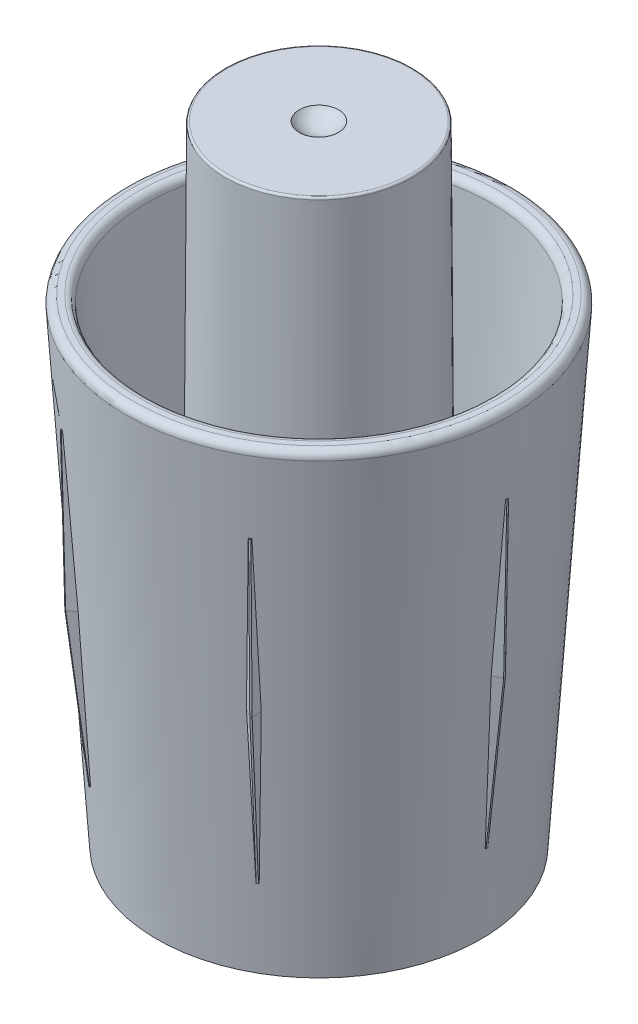
SolidWorks part; units mm, degrees
ref_plane "Front Plane" through (0, 0, 0) normal (0, 0, 1) x (1, 0, 0)
ref_plane "Top Plane" through (0, 0, 0) normal (0, 1, 0) x (1, 0, 0)
ref_plane "Right Plane" through (0, 0, 0) normal (1, 0, 0) x (0, 0, -1)
sketch "Sketch1" plane through (0, 0, 0) normal (0, 0, 1) x (1, 0, 0)
  line L0 (0, 0) -> (7.79, 0)
  line L1 (7.79, 0) -> (9.3, 22.95)
  line L2 (9.3, 22.95) -> (8.3, 22.95)
  line L3 (8.3, 22.95) -> (7.3459, 8.4492)
  line L4 (7.3459, 8.4492) -> (4.6, 13.16)
  line L5 (4.6, 13.16) -> (4.5, 30.16)
  line L6 (4.5, 30.16) -> (0, 30.16)
  line L7 (0, 30.16) -> (0, 29.16)
  line L8 (0, 29.16) -> (3.5, 29.16)
  line L9 (3.5, 29.16) -> (3.5941, 13.16)
  line L10 (3.5941, 13.16) -> (7.1848, 7)
  line L11 (7.1848, 7) -> (6.79, 1)
  line L12 (6.79, 1) -> (0, 1)
  line L13 (0, 1) -> (0, 0)
  dimension "D1" = 30.16
  dimension "D2" = 4.5
  dimension "D3" = 3.5
  dimension "D4" = 22.95
  dimension "D5" = 1
  dimension "D6" = 4.6
  dimension "D7" = 1
  dimension "D8" = 7.79
  dimension "D9" = 6.79
  dimension "D10" = 1
  dimension "D11" = 7
  dimension "D12" = 17
  dimension "D13" = 16
  dimension "D14" = 9.3
revolve "Revolve1" add sketch "Sketch1" angle 360 about L7
sketch "Sketch3" plane through (0, 0, 0) normal (0, 0, 1) x (1, 0, 0)
  line L0 (8.8104, 18.97) -> (8.6552, 11.47)
  line L1 (8.6552, 11.47) -> (7.8114, 3.97)
  line L2 (9.3, 22.95) -> (-9.3, 22.95) construction
  dimension "D1" = 15
  dimension "D2" = 7.5
  dimension "D3" = 3.98
ref_plane "Plane1" through (8.8104, 18.97, 0) normal (-0.0207, -0.9998, 0) x (-0.9998, 0.0207, 0)
sketch "Sketch4" plane through (8.8104, 18.97, 0) normal (-0.0207, -0.9998, 0) x (-0.9998, 0.0207, 0)
  line L1 (-0.266, -0.0413) -> (0.1711, -0.2936)
  line L2 (0.1711, -0.2936) -> (0.1711, 0.2936)
  line L3 (0.1711, 0.2936) -> (-0.266, 0.0413)
  circle A0 centre (0.0016, 0) radius 0.1695 construction
  arc A1 (-0.266, 0.0413) -> (-0.266, -0.0413) centre (-0.2248, 0) ccw
sweep "Sweep1" add profiles "Sketch4" path "Sketch3"
pattern_circular "CirPattern1" count 6 over 360 about axis through (0, 0, 0) along (0, 1, 0) of "Sweep1"
sketch "Sketch6" plane through (0, 0, 0) normal (0, -1, 0) x (-1, 0, 0)
  circle A0 centre (0, 0) radius 6.79
  dimension "D1" = 13.58
extrude "Cut-Extrude3" cut sketch "Sketch6" against normal blind 5
ref_plane "Plane2" through (0, 13.16, 0) normal (0, 1, 0) x (1, 0, 0)
sketch "Sketch7" plane through (0, 30.16, 0) normal (0, 1, 0) x (1, 0, 0)
  circle A0 centre (0, 0) radius 0.945
  point P3 (0.945, 0)
  point P4 (0, 0)
  dimension "D1" = 1.89
sketch "Sketch8" plane through (0, 0, 0) normal (0, 0, 1) x (1, 0, 0)
  line L0 (0, 30.16) -> (0, 29.71)
  line L1 (0.945, 30.16) -> (-0.945, 30.16) construction
  line L2 (0, 30.16) -> (0.945, 30.16)
  arc A0 (0, 29.71) -> (0.945, 30.16) centre (0, 30.9272) ccw
  dimension "D1" = 0.45
revolve "Cut-Revolve1" cut sketch "Sketch8" angle 360 about L0
sketch "Sketch9" plane through (0, 13.16, 0) normal (0, 1, 0) x (1, 0, 0)
  line L0 (0, 0) -> (0, 7.79) construction
  arc A0 (3.1615, 7.1196) -> (0.5166, 7.7729) centre (0, 0) ccw
  arc A1 (2.9585, 6.6627) -> (0.4834, 7.274) centre (0, 0) ccw
  arc A2 (-0.4834, 7.274) -> (-2.9585, 6.6627) centre (0, 0) ccw
  arc A3 (2.9585, 6.6627) -> (3.1615, 7.1196) centre (3.06, 6.8912) ccw
  arc A4 (0.5166, 7.7729) -> (0.4834, 7.274) centre (0.5, 7.5234) ccw
  arc A5 (-2.9585, 6.6627) -> (-3.1615, 7.1196) centre (-3.06, 6.8912) cw
  arc A6 (-0.5166, 7.7729) -> (-0.4834, 7.274) centre (-0.5, 7.5234) cw
  arc A7 (-0.5166, 7.7729) -> (-3.1615, 7.1196) centre (0, 0) ccw
  dimension "D1" = 15.58
  dimension "D2" = 14.58
  dimension "D4" = 2.56
  dimension "D5" = 0.5
sketch "Sketch10" plane through (0, 0, 0) normal (1, 0, 0) x (0, 0, -1)
  line L0 (7.136, 13.16) -> (6.4443, -0.0501)
  line L1 (7.7729, 13.16) -> (7.1196, 13.16) construction
  line L2 (0, 13.16) -> (7.79, 13.16) construction
sweep "Cut-Sweep1" cut profiles "Sketch9" path "Sketch10"
pattern_circular "CirPattern2" count 3 over 360 about axis through (0, 30.16, 0) along (0, 1, 0) of "Cut-Sweep1"
fillet "Fillet1" radius 0.1 1 edges at (-4.5, 30.16, 0)
fillet "Fillet2" radius 0.36 2 edges at (-9.3, 22.95, 0) (-8.3, 22.95, 0)
sketch "Sketch11" plane through (0, 0, 0) normal (0, 0, 1) x (1, 0, 0)
  line L0 (7.5658, 0) -> (6.8039, 3.1351)
  line L1 (-7.79, 0) -> (7.79, 0) construction
  line L2 (6.8039, 3.1351) -> (4.4119, 0)
  line L4 (4.4119, 0) -> (7.5658, 0)
  line L6 (0, 0) -> (0, 9.1685) construction
  line L7 (0, 13.16) -> (0, -0.0501) construction
revolve "Cut-Revolve2" cut sketch "Sketch11" angle 360 about L6
